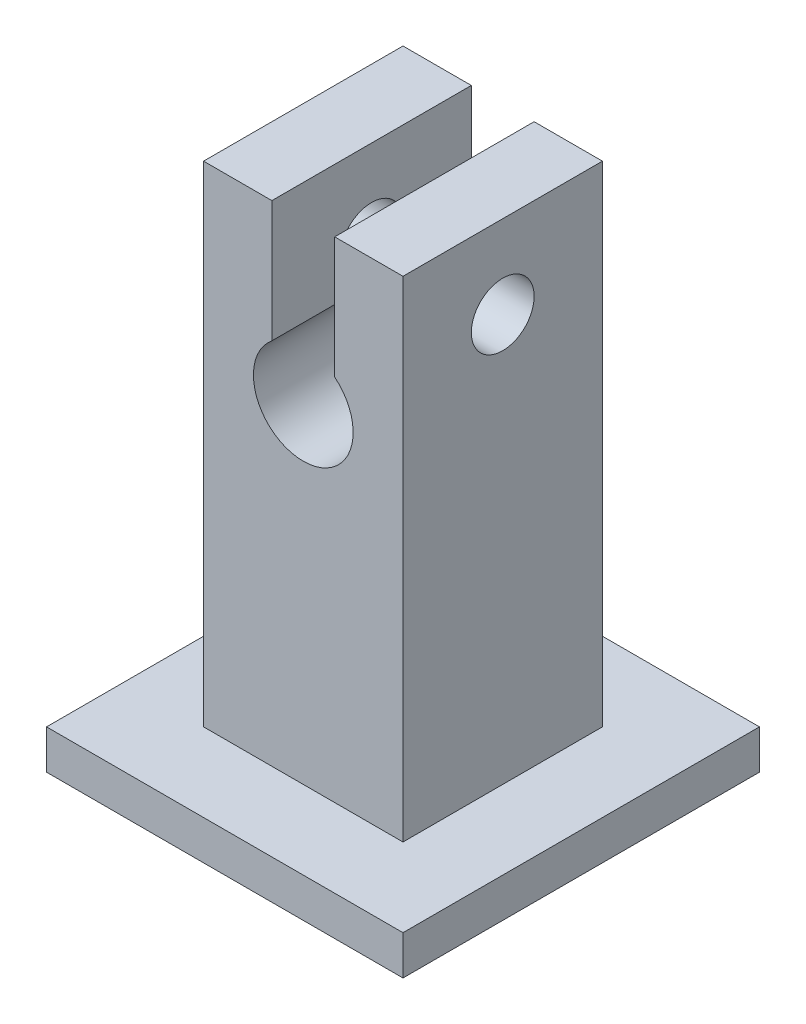
SolidWorks part; units mm, degrees
ref_plane "Front Plane" through (0, 0, 0) normal (0, 0, 1) x (1, 0, 0)
ref_plane "Top Plane" through (0, 0, 0) normal (0, 1, 0) x (1, 0, 0)
ref_plane "Right Plane" through (0, 0, 0) normal (1, 0, 0) x (0, 0, -1)
sketch "Sketch1" plane through (0, 0, 0) normal (0, 0, 1) x (1, 0, 0)
  line L0 (0, 0) -> (0, 31.2)
  line L1 (0, 31.2) -> (-4.35, 31.2)
  line L2 (-4.35, 31.2) -> (-4.35, 23.4659)
  line L3 (-8.35, 23.4659) -> (-8.35, 31.2)
  line L4 (-8.35, 31.2) -> (-12.7, 31.2)
  line L5 (-12.7, 31.2) -> (-12.7, 0)
  line L6 (-12.7, 0) -> (0, 0)
  arc A0 (-4.35, 23.4659) -> (-8.35, 23.4659) centre (-6.35, 21) cw
  dimension "D1" = 3.175
  dimension "D2" = 31.2
  dimension "D3" = 21
  dimension "D4" = 4
  dimension "D5" = 12.7
extrude "Boss-Extrude1" add sketch "Sketch1" along normal blind 12.7
sketch "Sketch2" plane through (0, 0, 0) normal (0, -1, 0) x (1, 0, 0)
  line L0 (-17.7, 6.35) -> (5, 6.35) construction
  line L1 (-17.7, 17.7) -> (5, 17.7)
  line L2 (-17.7, 17.7) -> (-17.7, -5)
  line L3 (-17.7, -5) -> (5, -5)
  line L4 (5, 17.7) -> (5, -5)
  line L5 (-6.35, 17.7) -> (-6.35, -5) construction
  line L6 (-12.7, 12.7) -> (0, 12.7) construction
  line L7 (-12.7, 12.7) -> (-12.7, 0) construction
  point P11 (-6.35, 12.7)
  point P14 (-12.7, 6.35)
  dimension "D1" = 22.7
extrude "Boss-Extrude2" add sketch "Sketch2" along normal blind 2.5
sketch "Sketch3" plane through (0, 0, 0) normal (1, 0, 0) x (0, 0, -1)
  line L1 (-22.0643, 20.6454) -> (10.279, 20.6454) construction
  line L2 (-12.7, 23.4659) -> (-12.7, 17.825) construction
  line L3 (-12.7, 31.2) -> (0, 31.2) construction
  circle A0 centre (-6.35, 25.9204) radius 2
  point P6 (-12.7, 20.6454)
  point P9 (-6.35, 31.2)
  dimension "D2" = 4
  dimension "D1" = 5.275
extrude "Cut-Extrude1" cut sketch "Sketch3" against normal through all
